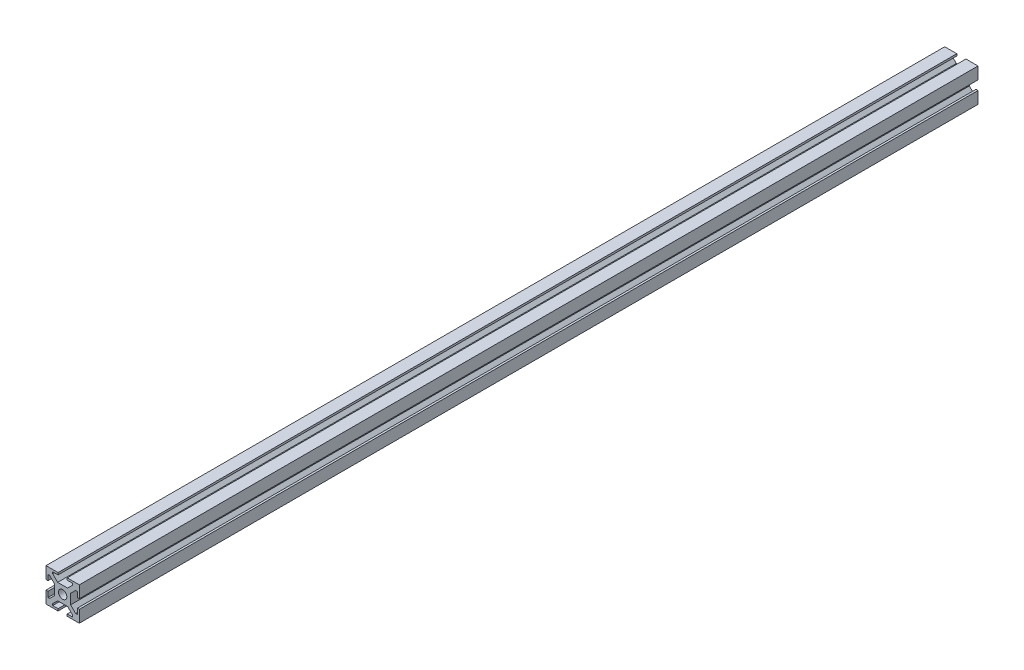
SolidWorks part; units mm, degrees
ref_plane "Plan de face" through (0, 0, 0) normal (0, 0, 1) x (1, 0, 0)
ref_plane "Plan de dessus" through (0, 0, 0) normal (0, 1, 0) x (1, 0, 0)
ref_plane "Plan de droite" through (0, 0, 0) normal (1, 0, 0) x (0, 0, -1)
sketch "Esquisse1" plane through (0, 0, 0) normal (0, 0, 1) x (1, 0, 0)
  line L1 (-22.5051, 0.0904) -> (-2.5051, 0.0904)
  line L2 (-22.5051, 0.0904) -> (-22.5051, -19.9096)
  line L3 (-22.5051, -19.9096) -> (-2.5051, -19.9096)
  line L4 (-2.5051, 0.0904) -> (-2.5051, -19.9096)
  dimension "D1" = 20
  dimension "D2" = 20
extrude "Boss.-Extru.1" add sketch "Esquisse1" along normal blind 540
sketch "Esquisse2" plane through (0, 0, 540) normal (0, 0, 1) x (1, 0, 0)
  line L0 (-22.5051, 0.0904) -> (-22.5051, -19.9096) construction
  line L1 (-22.5051, -7.1596) -> (-21.3051, -7.1596)
  line L2 (-22.5051, -7.1596) -> (-22.5051, -12.6596)
  line L3 (-22.5051, -12.6596) -> (-21.3051, -12.6596)
  line L4 (-21.3051, -7.1596) -> (-21.3051, -12.6596)
  line L5 (-2.5051, 0.0904) -> (-22.5051, 0.0904) construction
  line L6 (-15.2551, 0.0904) -> (-9.7551, 0.0904)
  line L7 (-15.2551, 0.0904) -> (-15.2551, -1.1096)
  line L8 (-15.2551, -1.1096) -> (-9.7551, -1.1096)
  line L9 (-9.7551, 0.0904) -> (-9.7551, -1.1096)
  line L10 (-2.5051, -19.9096) -> (-2.5051, 0.0904) construction
  line L11 (-2.5051, -7.1596) -> (-3.7051, -7.1596)
  line L12 (-2.5051, -7.1596) -> (-2.5051, -12.6596)
  line L13 (-2.5051, -12.6596) -> (-3.7051, -12.6596)
  line L14 (-3.7051, -7.1596) -> (-3.7051, -12.6596)
  line L15 (-22.5051, -19.9096) -> (-2.5051, -19.9096) construction
  line L16 (-15.2551, -19.9096) -> (-9.7551, -19.9096)
  line L17 (-15.2551, -19.9096) -> (-15.2551, -18.7096)
  line L18 (-15.2551, -18.7096) -> (-9.7551, -18.7096)
  line L19 (-9.7551, -19.9096) -> (-9.7551, -18.7096)
  dimension "D1" = 1.2
  dimension "D2" = 1.2
  dimension "D3" = 1.2
  dimension "D4" = 1.2
  dimension "D5" = 5.5
  dimension "D6" = 5.5
  dimension "D7" = 5.5
  dimension "D8" = 5.5
  dimension "D9" = 7.25
  dimension "D10" = 7.25
  dimension "D11" = 7.25
  dimension "D12" = 7.25
extrude "Enlèv. mat.-Extru.1" cut sketch "Esquisse2" against normal through all
sketch "Esquisse3" plane through (0, 0, 540) normal (0, 0, 1) x (1, 0, 0)
  line L0 (-15.2551, 0.0904) -> (-22.5051, 0.0904) construction
  line L1 (-21.3051, -15.9096) -> (-20.3051, -15.9096)
  line L2 (-21.3051, -15.9096) -> (-21.3051, -3.9096)
  line L3 (-21.3051, -3.9096) -> (-20.3051, -3.9096)
  line L4 (-17.3051, -12.9096) -> (-17.3051, -6.9096)
  line L5 (-18.5051, -1.1096) -> (-6.5051, -1.1096)
  line L6 (-18.5051, -1.1096) -> (-18.5051, -2.1096)
  line L7 (-15.5051, -5.1096) -> (-9.5051, -5.1096)
  line L8 (-6.5051, -1.1096) -> (-6.5051, -2.1096)
  line L9 (-3.7051, -3.9096) -> (-4.7051, -3.9096)
  line L10 (-3.7051, -3.9096) -> (-3.7051, -15.9096)
  line L11 (-3.7051, -15.9096) -> (-4.7051, -15.9096)
  line L12 (-7.7051, -6.9096) -> (-7.7051, -12.9096)
  line L13 (-6.5051, -18.7096) -> (-18.5051, -18.7096)
  line L14 (-6.5051, -18.7096) -> (-6.5051, -17.7096)
  line L15 (-9.5051, -14.7096) -> (-15.5051, -14.7096)
  line L16 (-18.5051, -18.7096) -> (-18.5051, -17.7096)
  line L17 (-2.5051, -7.1596) -> (-2.5051, 0.0904) construction
  line L18 (-15.2551, -1.1096) -> (-9.7551, -1.1096) construction
  line L19 (-3.7051, -7.1596) -> (-3.7051, -12.6596) construction
  line L20 (-9.7551, -19.9096) -> (-2.5051, -19.9096) construction
  line L21 (-22.5051, -12.6596) -> (-22.5051, -19.9096) construction
  line L22 (-22.5051, -19.9096) -> (-15.2551, -19.9096) construction
  line L23 (-15.5051, -14.7096) -> (-18.5051, -17.7096)
  line L24 (-20.3051, -15.9096) -> (-17.3051, -12.9096)
  line L25 (-6.5051, -17.7096) -> (-9.5051, -14.7096)
  line L26 (-4.7051, -15.9096) -> (-7.7051, -12.9096)
  line L27 (-4.7051, -3.9096) -> (-7.7051, -6.9096)
  line L28 (-9.5051, -5.1096) -> (-6.5051, -2.1096)
  line L29 (-18.5051, -2.1096) -> (-15.5051, -5.1096)
  line L30 (-20.3051, -3.9096) -> (-17.3051, -6.9096)
  point P1 (-17.3051, -3.9096)
  point P3 (-17.3051, -15.9096)
  point P5 (-6.5051, -5.1096)
  point P6 (-18.5051, -5.1096)
  point P9 (-7.7051, -15.9096)
  point P11 (-7.7051, -3.9096)
  point P13 (-18.5051, -14.7096)
  point P14 (-6.5051, -14.7096)
  point P24 (-6.1301, -19.9096)
  dimension "D1" = 4
  dimension "D2" = 4
  dimension "D3" = 4
  dimension "D4" = 4
  dimension "D5" = 12
  dimension "D6" = 4
  dimension "D7" = 12
  dimension "D8" = 4
  dimension "D9" = 0
  dimension "D10" = 0
  dimension "D11" = 4
  dimension "D12" = 12
  dimension "D13" = 12
  dimension "D14" = 4
  dimension "D15" = 1.2
  dimension "D16" = 1.2
  dimension "D17" = 3
  dimension "D18" = 3
  dimension "D19" = 3
  dimension "D20" = 3
  dimension "D21" = 3
  dimension "D22" = 3
  dimension "D23" = 3
  dimension "D24" = 3
  dimension "D25" = 3
  dimension "D26" = 3
  dimension "D27" = 3
  dimension "D28" = 3
  dimension "D29" = 3
  dimension "D30" = 3
  dimension "D31" = 3
  dimension "D32" = 3
extrude "Enlèv. mat.-Extru.2" cut sketch "Esquisse3" against normal through all
sketch "Esquisse4" plane through (0, 0, 540) normal (0, 0, 1) x (1, 0, 0)
  line L0 (-15.5051, -5.1096) -> (-9.5051, -5.1096) construction
  line L2 (-17.3051, -12.9096) -> (-17.3051, -6.9096) construction
  circle A0 centre (-12.5051, -9.9096) radius 2.5
  dimension "D1" = 5
  dimension "D2" = 4.8
  dimension "D3" = 4.8
extrude "Enlèv. mat.-Extru.3" cut sketch "Esquisse4" against normal through all
